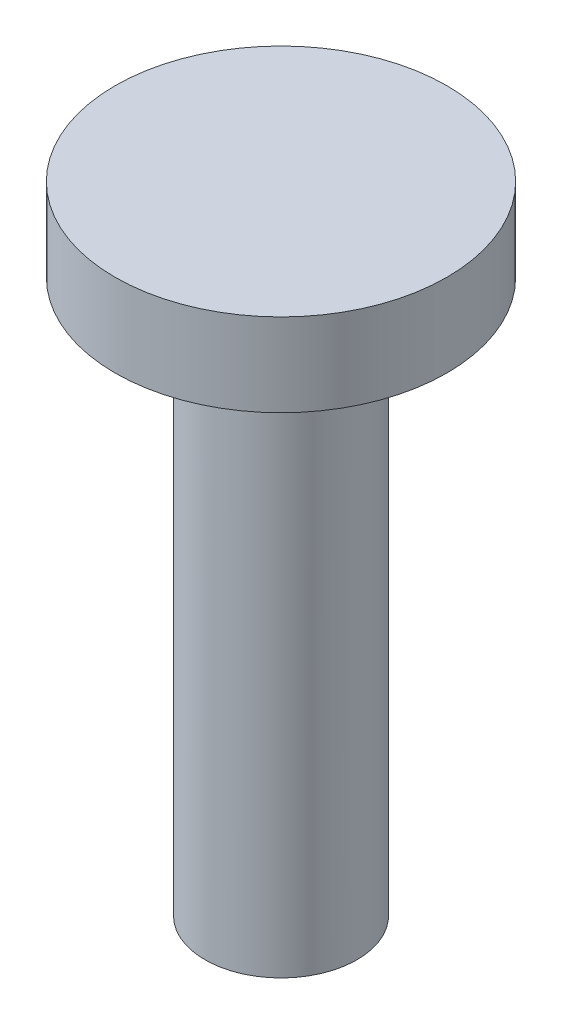
SolidWorks part; units mm, degrees
ref_plane "Front" through (0, 0, 0) normal (0, 0, 1) x (1, 0, 0)
ref_plane "Top" through (0, 0, 0) normal (0, 1, 0) x (1, 0, 0)
ref_plane "Right" through (0, 0, 0) normal (1, 0, 0) x (0, 0, -1)
sketch "Sketch1" plane through (0, 0, 0) normal (0, 1, 0) x (1, 0, 0)
  circle A0 centre (0, 0) radius 10
  dimension "D1" = 20
extrude "Boss-Extrude1" add sketch "Sketch1" along normal blind 66.6667
scale "축척1" scale about centroid uniform scaling yes scale factor 0.3
sketch "스케치1" plane through (0, 43.3333, 0) normal (0, 1, 0) x (1, 0, 0)
  circle A0 centre (0, 0) radius 6
  dimension "D1" = 12
extrude "보스-돌출1" add sketch "스케치1" along normal blind 3
sketch "스케치2" plane through (0, 23.3333, 0) normal (0, -1, 0) x (1, 0, 0)
  circle A0 centre (0, 0) radius 3
  circle A1 centre (0, 0) radius 2.75
  dimension "D1" = 6
  dimension "D2" = 0.25
extrude "컷-돌출1" cut sketch "스케치2" against normal up to surface (20 mm away) up to face at (0, 43.3333, 3)
